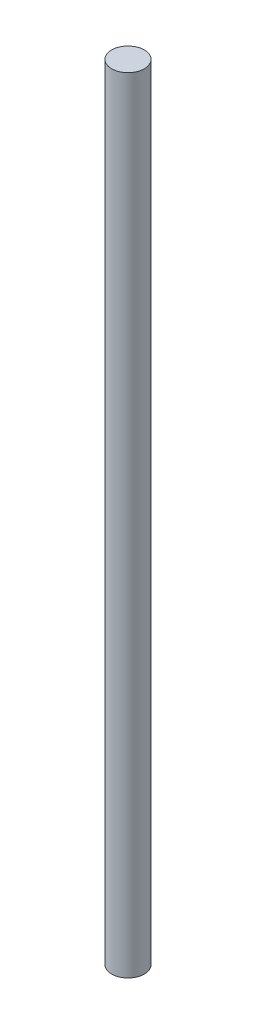
SolidWorks part; units mm, degrees
ref_plane "Front Plane" through (0, 0, 0) normal (0, 0, 1) x (1, 0, 0)
ref_plane "Top Plane" through (0, 0, 0) normal (0, 1, 0) x (1, 0, 0)
ref_plane "Right Plane" through (0, 0, 0) normal (1, 0, 0) x (0, 0, -1)
sketch "Sketch1" plane through (0, 0, 0) normal (0, 1, 0) x (1, 0, 0)
  circle A0 centre (0, 0) radius 3.175
  dimension "D1" = 6.35
extrude "Boss-Extrude1" add sketch "Sketch1" along normal blind 152.4
